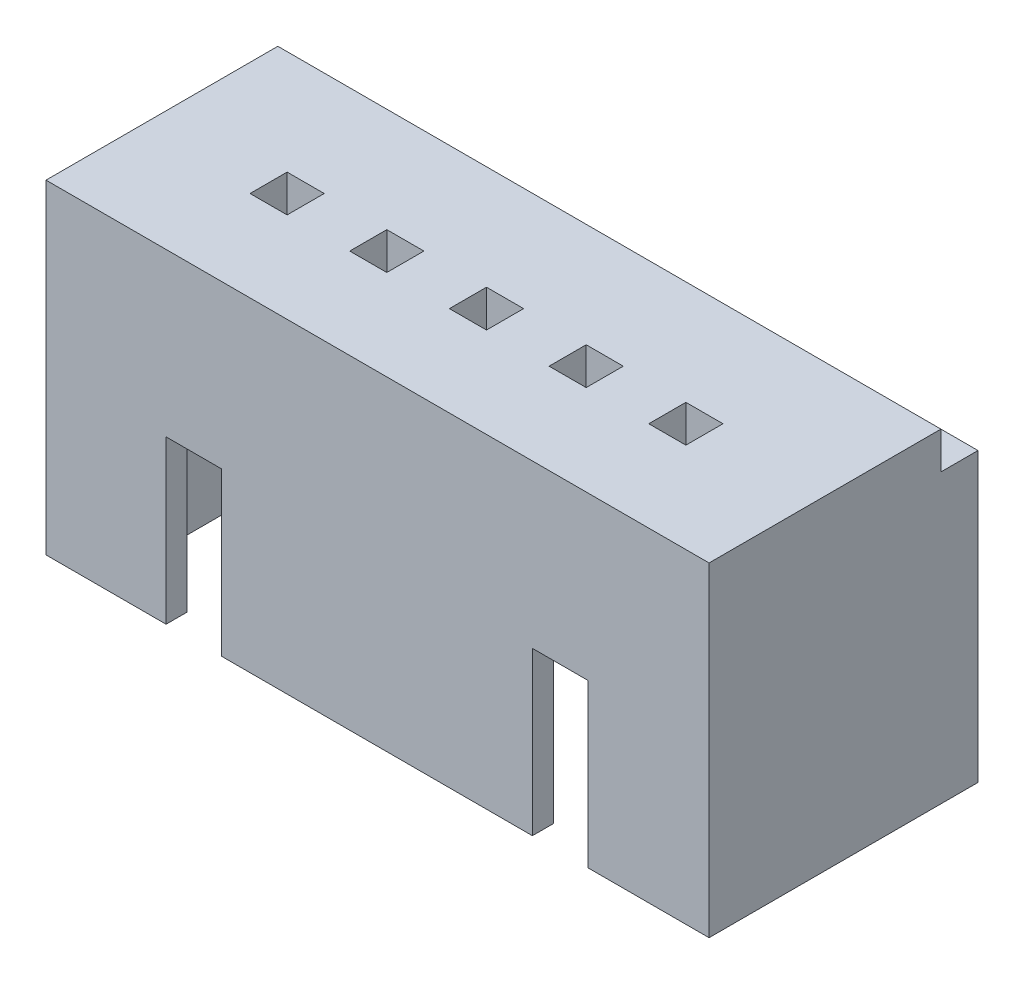
SolidWorks part; units mm, degrees
ref_plane "Front Plane" through (0, 0, 0) normal (0, 0, 1) x (1, 0, 0)
ref_plane "Top Plane" through (0, 0, 0) normal (0, 1, 0) x (1, 0, 0)
ref_plane "Right Plane" through (0, 0, 0) normal (1, 0, 0) x (0, 0, -1)
sketch "Sketch1" plane through (0, 0, 0) normal (0, 1, 0) x (1, 0, 0)
  line L1 (-7.15, -2.9) -> (7.15, -2.9)
  line L2 (-7.15, -2.9) -> (-7.15, 2.9)
  line L3 (-7.15, 2.9) -> (7.15, 2.9)
  line L4 (7.15, -2.9) -> (7.15, 2.9)
  line L5 (-7.15, -2.9) -> (7.15, 2.9) construction
  line L6 (-7.15, 2.9) -> (7.15, -2.9) construction
  point P0 (0, 0)
  dimension "D1" = 14.3
  dimension "D2" = 5.8
extrude "Boss-Extrude1" add sketch "Sketch1" along normal blind 7
sketch "Sketch3" plane through (0, 0, 0) normal (0, -1, 0) x (1, 0, 0)
  line L1 (-6, -2.45) -> (6, -2.45)
  line L2 (-6, -2.45) -> (-6, 2.45)
  line L3 (-6, 2.45) -> (6, 2.45)
  line L4 (6, -2.45) -> (6, 2.45)
  line L5 (-6, -2.45) -> (6, 2.45) construction
  line L6 (-6, 2.45) -> (6, -2.45) construction
  point P0 (0, 0)
  dimension "D1" = 12
  dimension "D2" = 4.9
extrude "Cut-Extrude1" cut sketch "Sketch3" against normal blind 5
sketch "Sketch4" plane through (0, 0, 2.9) normal (0, 0, 1) x (1, 0, 0)
  line L0 (-7.15, 0) -> (7.15, 0) construction
  line L1 (-4.56, 0) -> (-3.36, 0)
  line L2 (-4.56, 0) -> (-4.56, 3.5)
  line L3 (-4.56, 3.5) -> (-3.36, 3.5)
  line L4 (-3.36, 0) -> (-3.36, 3.5)
  line L6 (3.34, 0) -> (4.54, 0)
  line L7 (3.34, 0) -> (3.34, 3.5)
  line L8 (3.34, 3.5) -> (4.54, 3.5)
  line L9 (4.54, 0) -> (4.54, 3.5)
  dimension "D1" = 1.2
  dimension "D2" = 1.2
  dimension "D3" = 4.56
  dimension "D4" = 9.1
  dimension "D5" = 3.5
extrude "Cut-Extrude2" cut sketch "Sketch4" against normal blind 4
sketch "Sketch5" plane through (0, 7, 0) normal (0, 1, 0) x (1, 0, 0)
  line L0 (7.15, -2.9) -> (7.15, 2.9) construction
  line L1 (7.15, 2.1) -> (-7.15, 2.1)
  line L2 (7.15, 2.1) -> (7.15, 2.9)
  line L3 (7.15, 2.9) -> (-7.15, 2.9)
  line L4 (-7.15, 2.1) -> (-7.15, 2.9)
  dimension "D1" = 0.8
extrude "Cut-Extrude3" cut sketch "Sketch5" against normal blind 0.8 contours L1 L4 L3 L2
sketch "Sketch6" plane through (0, 7, 0) normal (0, 1, 0) x (1, 0, 0)
  line L1 (4.7, -0.15) -> (3.9, -0.15) construction
  line L2 (4.7, -0.95) -> (3.9, -0.95)
  line L3 (4.7, -0.95) -> (4.7, -0.15)
  line L4 (4.7, -0.15) -> (3.9, -0.15)
  line L6 (3.9, -0.95) -> (3.9, -0.15)
  line L8 (2.55, -0.95) -> (1.75, -0.95)
  line L9 (2.55, -0.95) -> (2.55, -0.15)
  line L12 (2.55, -0.15) -> (1.75, -0.15)
  line L13 (1.75, -0.95) -> (1.75, -0.15)
  line L14 (0.4, -0.95) -> (-0.4, -0.95)
  line L15 (0.4, -0.95) -> (0.4, -0.15)
  line L16 (0.4, -0.15) -> (-0.4, -0.15)
  line L17 (-0.4, -0.95) -> (-0.4, -0.15)
  line L18 (-1.75, -0.95) -> (-2.55, -0.95)
  line L19 (-1.75, -0.95) -> (-1.75, -0.15)
  line L20 (-1.75, -0.15) -> (-2.55, -0.15)
  line L21 (-2.55, -0.95) -> (-2.55, -0.15)
  line L22 (-3.9, -0.95) -> (-4.7, -0.95)
  line L23 (-3.9, -0.95) -> (-3.9, -0.15)
  line L24 (-3.9, -0.15) -> (-4.7, -0.15)
  line L25 (-4.7, -0.95) -> (-4.7, -0.15)
extrude "Cut-Extrude4" cut sketch "Sketch6" against normal blind 10
sketch "Sketch7" plane through (0, 5, 0) normal (0, -1, 0) x (1, 0, 0)
  line L0 (6, -2.45) -> (6, 2.45) construction
  line L1 (-6, -2.45) -> (6, -2.45)
  line L2 (-6, -2.45) -> (-6, -1.45)
  line L3 (-6, -1.45) -> (6, -1.45)
  line L4 (6, -2.45) -> (6, -1.45)
  dimension "D1" = 1
extrude "Cut-Extrude5" cut sketch "Sketch7" against normal blind 0.3
